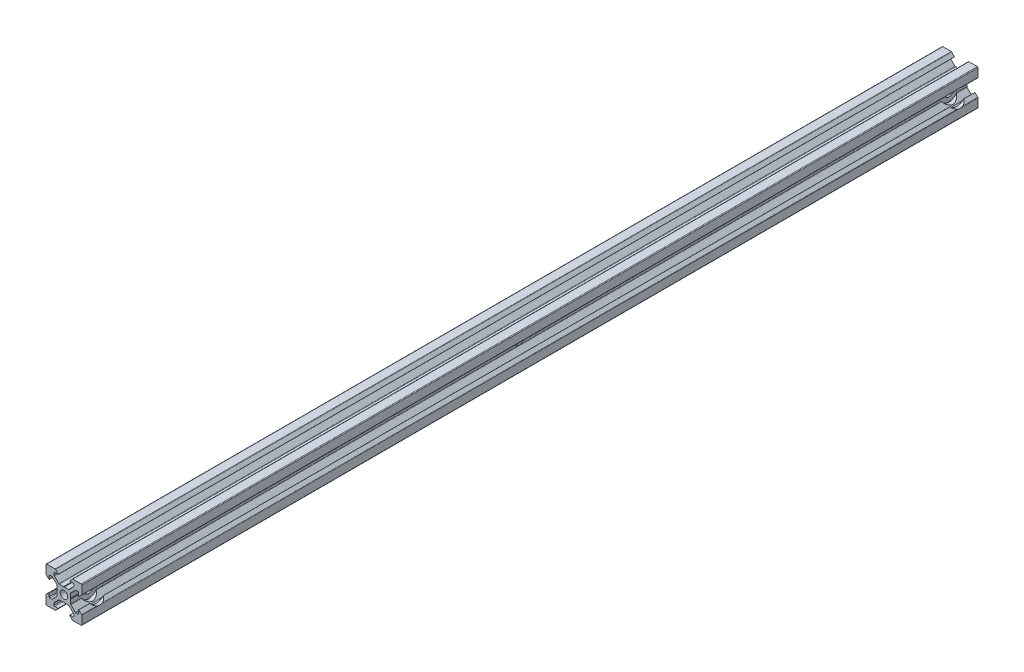
SolidWorks part; units mm, degrees
material "6063-T5"
ref_plane "前视基准面" through (0, 0, 0) normal (0, 0, 1) x (1, 0, 0)
ref_plane "上视基准面" through (0, 0, 0) normal (0, 1, 0) x (1, 0, 0)
ref_plane "右视基准面" through (0, 0, 0) normal (1, 0, 0) x (0, 0, -1)
sketch "草图1" plane through (0, 0, 0) normal (0, 0, 1) x (1, 0, 0)
  line L0 (0, 0) -> (13486.7145, 0) construction
  line L1 (0, 0) -> (0, 13486.7145) construction
  line L2 (0, 0) -> (9536.5473, 9536.5473) construction
  line L3 (0.2, 3.8) -> (2.5737, 3.8)
  line L4 (2.8565, 3.9172) -> (5.3828, 6.4435)
  line L5 (5.5, 6.7263) -> (5.5, 7.8)
  line L6 (5.1, 8.2) -> (3.2, 8.2)
  line L7 (3.1681, 8.2732) -> (4.6563, 9.8725)
  line L8 (4.9492, 10) -> (9.6, 10)
  line L9 (3.8, 0.2) -> (3.8, 2.5737)
  line L10 (3.9172, 2.8565) -> (6.4435, 5.3828)
  line L11 (6.7263, 5.5) -> (7.8, 5.5)
  line L12 (8.2, 5.1) -> (8.2, 3.2)
  line L13 (8.2732, 3.1681) -> (9.8725, 4.6563)
  line L14 (10, 4.9492) -> (10, 9.6)
  line L15 (3.8, -0.2) -> (3.8, -2.5737)
  line L16 (3.9172, -2.8565) -> (6.4435, -5.3828)
  line L17 (6.7263, -5.5) -> (7.8, -5.5)
  line L18 (8.2, -5.1) -> (8.2, -3.2)
  line L19 (8.2732, -3.1681) -> (9.8725, -4.6563)
  line L20 (10, -4.9492) -> (10, -9.6)
  line L21 (4.9492, -10) -> (9.6, -10)
  line L22 (3.1681, -8.2732) -> (4.6563, -9.8725)
  line L23 (5.1, -8.2) -> (3.2, -8.2)
  line L24 (5.5, -6.7263) -> (5.5, -7.8)
  line L25 (2.8565, -3.9172) -> (5.3828, -6.4435)
  line L26 (0.2, -3.8) -> (2.5737, -3.8)
  line L27 (-0.2, -3.8) -> (-2.5737, -3.8)
  line L28 (-2.8565, -3.9172) -> (-5.3828, -6.4435)
  line L29 (-5.5, -6.7263) -> (-5.5, -7.8)
  line L30 (-5.1, -8.2) -> (-3.2, -8.2)
  line L31 (-3.1681, -8.2732) -> (-4.6563, -9.8725)
  line L32 (-4.9492, -10) -> (-9.6, -10)
  line L33 (-10, -4.9492) -> (-10, -9.6)
  line L34 (-8.2732, -3.1681) -> (-9.8725, -4.6563)
  line L35 (-8.2, -5.1) -> (-8.2, -3.2)
  line L36 (-6.7263, -5.5) -> (-7.8, -5.5)
  line L37 (-3.9172, -2.8565) -> (-6.4435, -5.3828)
  line L38 (-3.8, -0.2) -> (-3.8, -2.5737)
  line L39 (-3.8, 0.2) -> (-3.8, 2.5737)
  line L40 (-3.9172, 2.8565) -> (-6.4435, 5.3828)
  line L41 (-6.7263, 5.5) -> (-7.8, 5.5)
  line L42 (-8.2, 5.1) -> (-8.2, 3.2)
  line L43 (-8.2732, 3.1681) -> (-9.8725, 4.6563)
  line L44 (-10, 4.9492) -> (-10, 9.6)
  line L45 (-4.9492, 10) -> (-9.6, 10)
  line L46 (-3.1681, 8.2732) -> (-4.6563, 9.8725)
  line L47 (-5.1, 8.2) -> (-3.2, 8.2)
  line L48 (-5.5, 6.7263) -> (-5.5, 7.8)
  line L49 (-2.8565, 3.9172) -> (-5.3828, 6.4435)
  line L50 (-0.2, 3.8) -> (-2.5737, 3.8)
  line L51 (-3.2, 8.2) -> (-3.1681, 8.2732)
  line L52 (3.2, 8.2) -> (3.1681, 8.2732)
  line L53 (-8.2, 3.2) -> (-8.2732, 3.1681)
  line L54 (8.2, 3.2) -> (8.2732, 3.1681)
  line L55 (8.2, -3.2) -> (8.2732, -3.1681)
  line L56 (3.2, -8.2) -> (3.1681, -8.2732)
  line L57 (-3.2, -8.2) -> (-3.1681, -8.2732)
  line L58 (-8.2, -3.2) -> (-8.2732, -3.1681)
  line L59 (-0.2, 3.8) -> (0, 3.6)
  line L60 (0, 3.6) -> (0.2, 3.8)
  line L61 (3.8, 0.2) -> (3.6, 0)
  line L62 (3.6, 0) -> (3.8, -0.2)
  line L63 (0.2, -3.8) -> (0, -3.6)
  line L64 (0, -3.6) -> (-0.2, -3.8)
  line L65 (-3.8, -0.2) -> (-3.6, 0)
  line L66 (-3.6, 0) -> (-3.8, 0.2)
  arc A0 (-4.9492, 10) -> (-4.6563, 9.8725) centre (-4.9492, 9.6) cw
  arc A1 (-5.1, 8.2) -> (-5.5, 7.8) centre (-5.1, 7.8) ccw
  arc A2 (-5.5, 6.7263) -> (-5.3828, 6.4435) centre (-5.1, 6.7263) ccw
  arc A3 (-2.8565, 3.9172) -> (-2.5737, 3.8) centre (-2.5737, 4.2) ccw
  arc A4 (-10, 9.6) -> (-9.6, 10) centre (-9.6, 9.6) cw
  arc A5 (-9.8725, 4.6563) -> (-10, 4.9492) centre (-9.6, 4.9492) cw
  arc A6 (-7.8, 5.5) -> (-8.2, 5.1) centre (-7.8, 5.1) ccw
  arc A7 (-6.4435, 5.3828) -> (-6.7263, 5.5) centre (-6.7263, 5.1) ccw
  arc A8 (-3.8, 2.5737) -> (-3.9172, 2.8565) centre (-4.2, 2.5737) ccw
  arc A9 (-10, -4.9492) -> (-9.8725, -4.6563) centre (-9.6, -4.9492) cw
  arc A10 (-8.2, -5.1) -> (-7.8, -5.5) centre (-7.8, -5.1) ccw
  arc A11 (-6.7263, -5.5) -> (-6.4435, -5.3828) centre (-6.7263, -5.1) ccw
  arc A12 (-3.9172, -2.8565) -> (-3.8, -2.5737) centre (-4.2, -2.5737) ccw
  arc A13 (-9.6, -10) -> (-10, -9.6) centre (-9.6, -9.6) cw
  arc A14 (-4.6563, -9.8725) -> (-4.9492, -10) centre (-4.9492, -9.6) cw
  arc A15 (-5.5, -7.8) -> (-5.1, -8.2) centre (-5.1, -7.8) ccw
  arc A16 (-5.3828, -6.4435) -> (-5.5, -6.7263) centre (-5.1, -6.7263) ccw
  arc A17 (-2.5737, -3.8) -> (-2.8565, -3.9172) centre (-2.5737, -4.2) ccw
  arc A18 (4.9492, -10) -> (4.6563, -9.8725) centre (4.9492, -9.6) cw
  arc A19 (5.1, -8.2) -> (5.5, -7.8) centre (5.1, -7.8) ccw
  arc A20 (5.5, -6.7263) -> (5.3828, -6.4435) centre (5.1, -6.7263) ccw
  arc A21 (2.8565, -3.9172) -> (2.5737, -3.8) centre (2.5737, -4.2) ccw
  arc A22 (10, -9.6) -> (9.6, -10) centre (9.6, -9.6) cw
  arc A23 (9.8725, -4.6563) -> (10, -4.9492) centre (9.6, -4.9492) cw
  arc A24 (7.8, -5.5) -> (8.2, -5.1) centre (7.8, -5.1) ccw
  arc A25 (6.4435, -5.3828) -> (6.7263, -5.5) centre (6.7263, -5.1) ccw
  arc A26 (3.8, -2.5737) -> (3.9172, -2.8565) centre (4.2, -2.5737) ccw
  arc A27 (9.8725, 4.6563) -> (10, 4.9492) centre (9.6, 4.9492) ccw
  arc A28 (7.8, 5.5) -> (8.2, 5.1) centre (7.8, 5.1) cw
  arc A29 (6.4435, 5.3828) -> (6.7263, 5.5) centre (6.7263, 5.1) cw
  arc A30 (3.8, 2.5737) -> (3.9172, 2.8565) centre (4.2, 2.5737) cw
  arc A31 (9.6, 10) -> (10, 9.6) centre (9.6, 9.6) cw
  arc A32 (4.6563, 9.8725) -> (4.9492, 10) centre (4.9492, 9.6) cw
  arc A33 (5.5, 7.8) -> (5.1, 8.2) centre (5.1, 7.8) ccw
  arc A34 (5.3828, 6.4435) -> (5.5, 6.7263) centre (5.1, 6.7263) ccw
  arc A35 (2.5737, 3.8) -> (2.8565, 3.9172) centre (2.5737, 4.2) ccw
  circle A36 centre (0, 0) radius 2
  point P12 (3.1, 8.2)
  point P18 (8.2, 3.1)
  point P28 (8.2, -3.1)
  point P34 (3.1, -8.2)
  point P41 (-3.1, -8.2)
  point P47 (-8.2, -3.1)
  point P54 (-8.2, 3.1)
  point P60 (-3.1, 8.2)
  point P62 (0, 0)
  point P112 (10, 4.775)
  point P115 (8.2, 5.5)
  point P118 (6.5607, 5.5)
  point P121 (3.8, 2.7393)
  point P124 (10, 10)
  point P127 (4.775, 10)
  point P130 (5.5, 8.2)
  point P133 (5.5, 6.5607)
  point P136 (2.7393, 3.8)
  point P168 (0, 0)
  dimension "D9" = 0.4
  dimension "D23" = 4
  dimension "D1" = 5.5
  dimension "D2" = 10
  dimension "D3" = 3.1
  dimension "D4" = 1.5
  dimension "D5" = 1.8
  dimension "D7" = 7.6
  dimension "D11" = 20
  dimension "D12" = 45
  dimension "D13" = 0.4
  dimension "D8" = 4
  dimension "D14" = 4
extrude "凸台-拉伸1" add sketch "草图1" along normal blind 500
hole_wizard "Ø5.0 (5) 直径孔1" positions "草图8" profile "草图9" hole size "Ø5.0" standard "GB" end condition through all
sketch "草图8" plane through (10, 0, 0) normal (1, 0, 0) x (0, 0, -1)
  line L0 (-500, 0) -> (0, 0) construction
  line L1 (0, 4.9492) -> (0, 9.6) construction
  line L3 (-500, 4.9492) -> (-500, 9.6) construction
  point P0 (-490, 0)
  point P3 (-10, 0)
  dimension "D1" = 10
  dimension "D2" = 10
sketch "草图9" plane through (10, 0, 490) normal (0, 1, 0) x (0, 0, -1)
  line L0 (0, 0) -> (0, 20)
  line L1 (0, 20) -> (2.5, 20)
  line L2 (2.5, 20) -> (2.5, 0)
  line L5 (2.5, 0) -> (0, 0)
  line L11 (0, -6.35) -> (0, 107.95) construction
  dimension "通孔孔直径" = 5
  dimension "通孔孔深度" = 20
hole_wizard "Ø10.0 (10) 直径孔1" positions "草图10" profile "草图11" hole size "Ø10.0" standard "GB"
sketch "草图10" plane through (10, 0, 0) normal (1, 0, 0) x (0, 0, -1)
  point P0 (-490, 0)
  point P3 (-10, 0)
sketch "草图11" plane through (10, 0, 490) normal (0, 1, 0) x (0, 0, -1)
  line L0 (0, 0) -> (0, 6.2)
  line L1 (0, 6.2) -> (5, 6.2)
  line L2 (5, 6.2) -> (5, 0)
  line L5 (5, 0) -> (0, 0)
  line L10 (0, 6.2) -> (-5, 6.2) construction
  line L11 (0, -6.35) -> (0, 107.95) construction
  dimension "孔直径" = 10
  dimension "孔深度" = 6.2
  dimension "导头角度" = 180
hole_wizard "M5 螺纹孔1" positions "草图4" profile "草图5" tap size "M5" standard "GB"
sketch "草图4" plane through (0, 0, 0) normal (0, 0, -1) x (-1, 0, 0)
  point P0 (0, 0)
sketch "草图5" plane through (0, 0, 0) normal (1, 0, 0) x (0, 1, 0)
  line L0 (0, 0) -> (0, 10)
  line L1 (0, 10) -> (2.1, 10)
  line L2 (2.1, 10) -> (2.1, 0)
  line L5 (2.1, 0) -> (0, 0)
  line L10 (0, 10) -> (-2.1, 10) construction
  line L11 (0, -6.35) -> (0, 107.95) construction
  dimension "螺纹孔钻头直径" = 4.2
  dimension "螺纹孔钻头深度" = 10
  dimension "导头角度" = 180
cosmetic thread "孔螺蚊线1"
hole_wizard "M5 螺纹孔2" positions "草图6" profile "草图7" tap size "M5" standard "GB"
sketch "草图6" plane through (0, 0, 500) normal (0, 0, 1) x (1, 0, 0)
  point P0 (0, 0)
sketch "草图7" plane through (0, 0, 500) normal (1, 0, 0) x (0, -1, 0)
  line L0 (0, 0) -> (0, 10)
  line L1 (0, 10) -> (2.1, 10)
  line L2 (2.1, 10) -> (2.1, 0)
  line L5 (2.1, 0) -> (0, 0)
  line L10 (0, 10) -> (-2.1, 10) construction
  line L11 (0, -6.35) -> (0, 107.95) construction
  dimension "螺纹孔钻头直径" = 4.2
  dimension "螺纹孔钻头深度" = 10
  dimension "导头角度" = 180
cosmetic thread "孔螺蚊线2"
hole_wizard "M5 螺纹孔3" positions "草图12" profile "草图13" tap size "M5" standard "GB" end condition through all
sketch "草图12" plane through (3.8, 0, 0) normal (1, 0, 0) x (0, 0, -1)
  line L0 (-487.5, 0) -> (-12.5, 0) construction
  line L1 (0, 4.9492) -> (0, 9.6) construction
  point P0 (-250, 0)
  dimension "D1" = 250
sketch "草图13" plane through (3.8, 0, 250) normal (0, 1, 0) x (0, 0, -1)
  line L0 (0, 0) -> (0, 13.8)
  line L1 (0, 13.8) -> (2.1, 13.8)
  line L2 (2.1, 13.8) -> (2.1, 0.425)
  line L3 (2.1, 0.425) -> (2.525, 0)
  line L5 (2.525, 0) -> (0, 0)
  line L6 (-2.1, 0.425) -> (-2.525, 0) construction
  line L11 (0, -6.35) -> (0, 107.95) construction
  dimension "通孔螺纹孔钻头直径" = 4.2
  dimension "通孔螺纹孔钻头深度" = 13.8
  dimension "近端锥形沉头孔直径" = 5.05
  dimension "近端锥形沉头孔角度" = 90
cosmetic thread "孔螺蚊线3"
